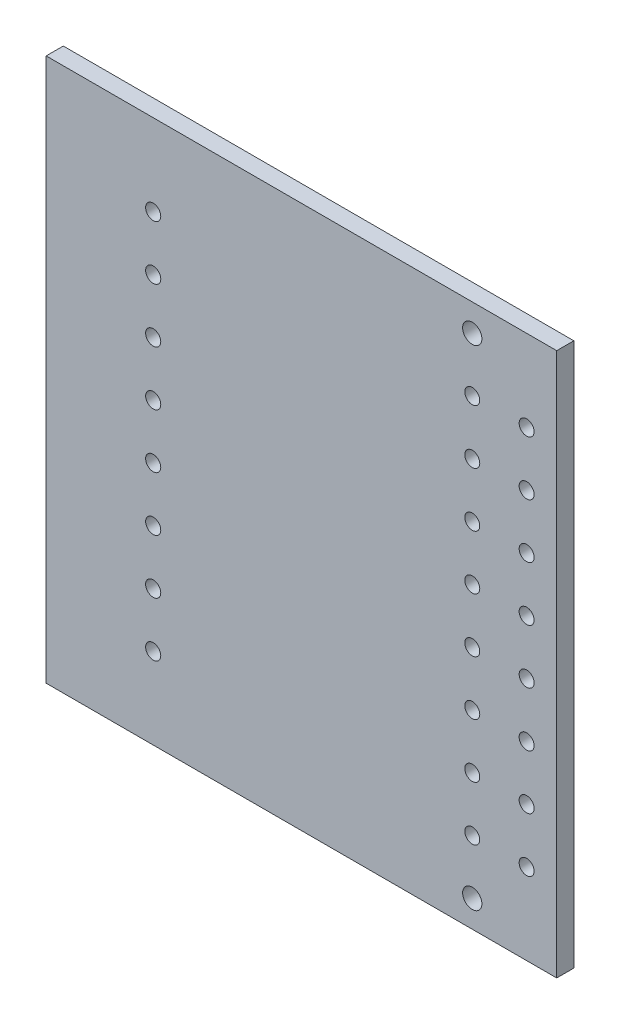
SolidWorks part; units mm, degrees
ref_plane "Front Plane" through (0, 0, 0) normal (0, 0, 1) x (1, 0, 0)
ref_plane "Top Plane" through (0, 0, 0) normal (0, 1, 0) x (1, 0, 0)
ref_plane "Right Plane" through (0, 0, 0) normal (1, 0, 0) x (0, 0, -1)
sketch "Sketch1" plane through (0, 0, 0) normal (0, 0, 1) x (1, 0, 0)
  line L1 (-147.6714, -52.8472) -> (-99.9714, -52.8472)
  line L2 (-147.6714, -52.8472) -> (-147.6714, -2.0872)
  line L3 (-147.6714, -2.0872) -> (-99.9714, -2.0872)
  line L4 (-99.9714, -52.8472) -> (-99.9714, -2.0872)
  circle A0 centre (-107.8614, -45.2672) radius 0.7
  circle A1 centre (-102.7814, -45.2672) radius 0.7
  circle A2 centre (-102.7814, -40.1872) radius 0.7
  circle A3 centre (-102.7814, -35.1072) radius 0.7
  circle A4 centre (-102.7814, -30.0272) radius 0.7
  circle A5 centre (-102.7814, -24.9472) radius 0.7
  circle A6 centre (-102.7814, -19.8672) radius 0.7
  circle A7 centre (-102.7814, -14.7872) radius 0.7
  circle A8 centre (-102.7814, -9.7072) radius 0.7
  circle A9 centre (-107.8614, -40.1872) radius 0.7
  circle A10 centre (-107.8614, -35.1072) radius 0.7
  circle A11 centre (-107.8614, -30.0272) radius 0.7
  circle A12 centre (-107.8614, -24.9472) radius 0.7
  circle A13 centre (-107.8614, -19.8672) radius 0.7
  circle A14 centre (-107.8614, -14.7872) radius 0.7
  circle A15 centre (-107.8614, -9.7072) radius 0.7
  circle A16 centre (-137.6714, -45.2672) radius 0.7071
  circle A17 centre (-137.6714, -40.1872) radius 0.7071
  circle A18 centre (-137.6714, -35.1072) radius 0.7071
  circle A19 centre (-137.6714, -30.0272) radius 0.7071
  circle A20 centre (-137.6714, -24.9472) radius 0.7071
  circle A21 centre (-137.6714, -19.8672) radius 0.7071
  circle A22 centre (-137.6714, -14.7872) radius 0.7071
  circle A23 centre (-137.6714, -9.7072) radius 0.7071
  circle A24 centre (-107.8614, -50.3472) radius 0.9
  circle A25 centre (-107.8614, -4.6272) radius 0.9
  dimension "D1" = 2
  dimension "D2" = 8
  dimension "D3" = 8
extrude "Boss-Extrude1" add sketch "Sketch1" along normal blind 1.6
